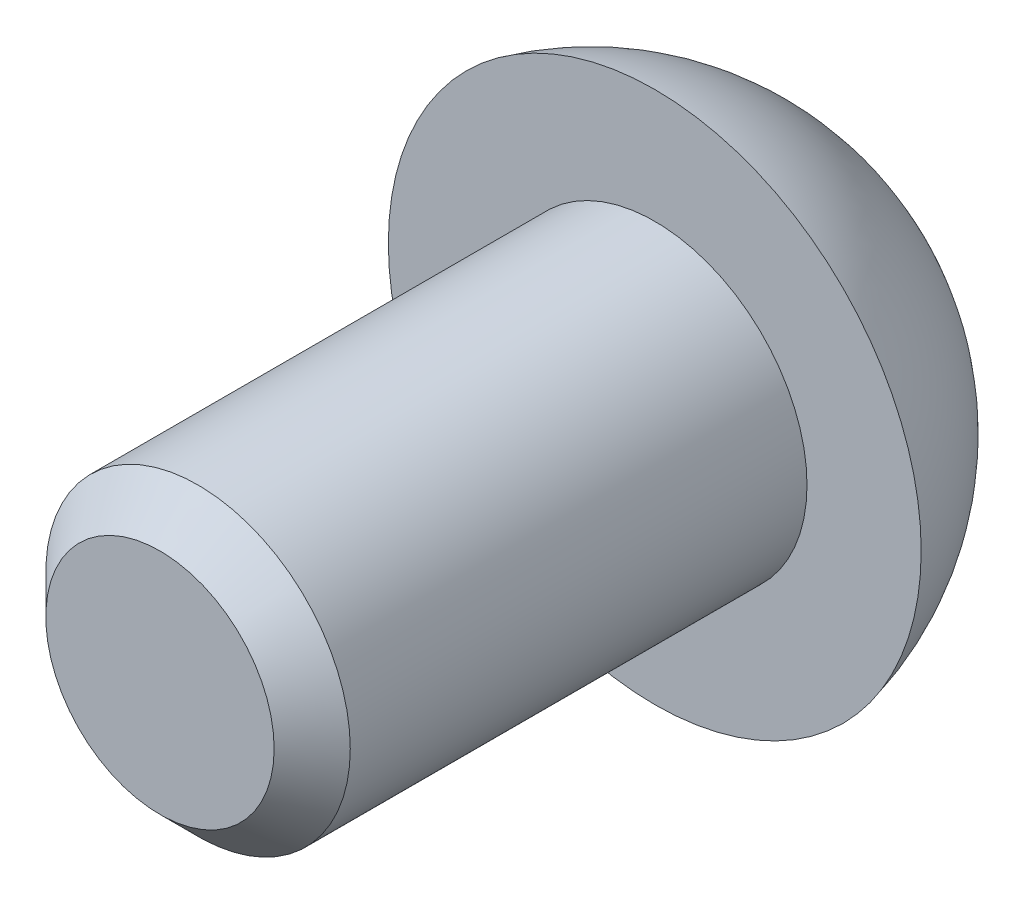
SolidWorks part; units mm, degrees
ref_plane "Front Plane" through (0, 0, 0) normal (0, 0, 1) x (1, 0, 0)
ref_plane "Top Plane" through (0, 0, 0) normal (0, 1, 0) x (1, 0, 0)
ref_plane "Right Plane" through (0, 0, 0) normal (1, 0, 0) x (0, 0, -1)
sketch "Sketch1" plane through (0, 0, 0) normal (0, 0, 1) x (1, 0, 0)
  circle A0 centre (0, 0) radius 2
  dimension "D1" = 4
extrude "Boss-Extrude1" add sketch "Sketch1" against normal blind 6.5
chamfer "Chamfer1" distance 0.5 angle 45 1 edges at (2, 0, 0)
sketch "Sketch2" plane through (0, 0, 0) normal (1, 0, 0) x (0, 0, -1)
  line L0 (3.7426, 0) -> (9.2574, 0) construction
  line L1 (6.5, 0) -> (6.5, 3.5)
  line L2 (6.5, -2) -> (6.5, 2) construction
  line L3 (9.2574, 0) -> (6.5, 0)
  arc A0 (6.5, 3.5) -> (9.2574, 0) centre (5.6574, 0) cw
  point P9 (0, 0)
  point P10 (0, 0)
  dimension "D2" = 3.6
  dimension "D1" = 3.5
revolve "Revolve1" add sketch "Sketch2" angle 360 about L0
